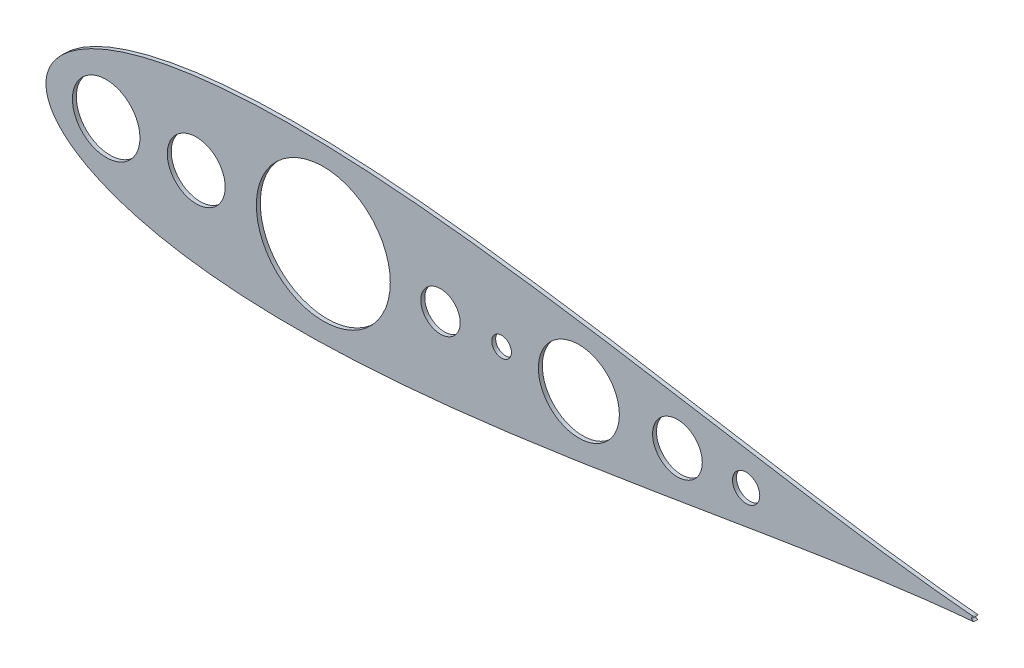
SolidWorks part; units mm, degrees
ref_plane "Front Plane" through (0, 0, 0) normal (0, 0, 1) x (1, 0, 0)
ref_plane "Top Plane" through (0, 0, 0) normal (0, 1, 0) x (1, 0, 0)
ref_plane "Right Plane" through (0, 0, 0) normal (1, 0, 0) x (0, 0, -1)
sketch "Model" plane through (0, 0, 0) normal (0, 0, 1) x (1, 0, 0)
  line L0 (786.347, 515.344) -> (786.347, 515.865)
  line L1 (784.9141, 514.1717) -> (785.37, 514.1717)
  line L2 (785.5654, 516.7117) -> (785.1095, 516.7117)
  line L3 (784.0675, 516.0604) -> (783.1903, 516.0604)
  line L4 (784.0675, 516.386) -> (784.0675, 516.0604)
  line L5 (783.2391, 516.386) -> (784.0675, 516.386)
  line L6 (783.4834, 518.0142) -> (783.2391, 516.386)
  line L7 (783.0906, 518.0142) -> (783.4834, 518.0142)
  line L8 (782.8463, 516.386) -> (783.0906, 518.0142)
  line L9 (782.0505, 518.0142) -> (781.8063, 516.386)
  line L10 (781.6577, 518.0142) -> (782.0505, 518.0142)
  line L11 (781.4135, 516.386) -> (781.6577, 518.0142)
  line L12 (780.4203, 516.386) -> (781.4135, 516.386)
  line L13 (780.4203, 516.0604) -> (780.4203, 516.386)
  line L14 (781.3647, 516.0604) -> (780.4203, 516.0604)
  line L15 (781.1886, 514.8881) -> (781.3647, 516.0604)
  line L16 (780.29, 514.8881) -> (781.1886, 514.8881)
  line L17 (780.29, 514.5625) -> (780.29, 514.8881)
  line L18 (781.1398, 514.5625) -> (780.29, 514.5625)
  line L19 (780.8762, 512.804) -> (781.1398, 514.5625)
  line L20 (781.27, 512.804) -> (780.8762, 512.804)
  line L21 (781.5336, 514.5625) -> (781.27, 512.804)
  line L22 (782.5726, 514.5625) -> (781.5336, 514.5625)
  line L23 (782.309, 512.804) -> (782.5726, 514.5625)
  line L24 (782.7028, 512.804) -> (782.309, 512.804)
  line L25 (782.9664, 514.5625) -> (782.7028, 512.804)
  line L26 (783.9372, 514.5625) -> (782.9664, 514.5625)
  line L27 (783.9372, 514.8881) -> (783.9372, 514.5625)
  line L28 (783.0153, 514.8881) -> (783.9372, 514.8881)
  line L29 (783.1903, 516.0604) -> (783.0153, 514.8881)
  line L30 (781.8063, 516.386) -> (782.8463, 516.386)
  line L31 (781.5824, 514.8881) -> (782.6214, 514.8881)
  line L32 (782.7975, 516.0604) -> (781.7575, 516.0604)
  line L33 (782.6214, 514.8881) -> (782.7975, 516.0604)
  line L34 (781.7575, 516.0604) -> (781.5824, 514.8881)
  circle A0 centre (390.1313, 511.9487) radius 18.669
  circle A1 centre (547.6113, 511.9487) radius 12.7
  circle A2 centre (586.9813, 511.9487) radius 6.35
  circle A3 centre (700.3234, 511.9487) radius 16.0288
  circle A4 centre (744.6175, 511.9487) radius 8.7799
  circle A5 centre (332.0731, 511.9487) radius 21.7634
  arc A6 (890.8162, 510.4774) -> (891.5484, 510.7448) centre (890.6938, 511.9487) ccw
  arc A7 (891.5489, 513.1522) -> (890.8162, 513.42) centre (890.6938, 511.9487) ccw
  arc A8 (891.5489, 513.1522) -> (891.5484, 510.7448) centre (891.2322, 511.9485) ccw
  circle A9 centre (636.7879, 511.9487) radius 26.1032
  circle A10 centre (472.0506, 511.9487) radius 43.167
  spline S0 degree 3 poles (890.8162, 513.42) (890.3349, 513.46) (886.7082, 513.7655) (879.5659, 514.4256) (868.9642, 515.5285) (857.2098, 516.8818) (844.3469, 518.4937) (830.4355, 520.3658) (815.5358, 522.4939) (799.7123, 524.867) (783.0322, 527.4682) (765.5654, 530.2744) (747.384, 533.2565) (728.5623, 536.3802) (709.1765, 539.6059) (689.3045, 542.8901) (669.0255, 546.185) (648.4208, 549.44) (627.5727, 552.6022) (606.5651, 555.6172) (585.4835, 558.4299) (564.4149, 560.9854) (543.4476, 563.23) (522.6717, 565.1117) (502.1785, 566.5817) (482.061, 567.5944) (462.4138, 568.109) (443.3327, 568.0899) (424.9152, 567.5068) (407.2601, 566.3367) (390.4682, 564.5628) (374.6421, 562.177) (359.8874, 559.1785) (346.3131, 555.5773) (334.0341, 551.3946) (323.1728, 546.6676) (313.8611, 541.4589) (306.2382, 535.8742) (300.4324, 530.0959) (296.5018, 524.4296) (294.31, 519.3174) (293.4249, 515.2165) (293.2233, 511.9487) (293.4249, 508.6808) (294.31, 504.5799) (296.5018, 499.4677) (300.4324, 493.8014) (306.2382, 488.0231) (313.8611, 482.4384) (323.1728, 477.2297) (334.0341, 472.5027) (346.3131, 468.32) (359.8874, 464.7188) (374.6421, 461.7204) (390.4682, 459.3346) (407.2601, 457.5606) (424.9152, 456.3906) (443.3327, 455.8074) (462.4138, 455.7883) (482.061, 456.3029) (502.1785, 457.3157) (522.6717, 458.7856) (543.4476, 460.6673) (564.4149, 462.9119) (585.4835, 465.4674) (606.5651, 468.2801) (627.5727, 471.2951) (648.4208, 474.4573) (669.0255, 477.7124) (689.3045, 481.0073) (709.1765, 484.2914) (728.5623, 487.5172) (747.384, 490.6408) (765.5654, 493.6229) (783.0322, 496.4291) (799.7123, 499.0303) (815.5358, 501.4035) (830.4355, 503.5316) (844.3469, 505.4037) (857.2098, 507.0155) (868.9642, 508.3689) (879.5659, 509.4717) (886.7082, 510.1319) (890.3349, 510.4373) (890.8162, 510.4774) knots 0.020157 0.020157 0.020157 0.020157 0.021271 0.028553 0.036781 0.04592 0.055932 0.066773 0.078397 0.090755 0.103793 0.117456 0.131686 0.146422 0.1616 0.177156 0.193024 0.209135 0.225421 0.241812 0.258238 0.274629 0.290914 0.307025 0.322893 0.338448 0.353626 0.368361 0.38259 0.396253 0.40929 0.421647 0.43327 0.444109 0.454119 0.463255 0.471479 0.478755 0.485052 0.490344 0.49461 0.497833 0.5 0.502167 0.50539 0.509656 0.514948 0.521245 0.528521 0.536745 0.545881 0.555891 0.56673 0.578353 0.59071 0.603747 0.61741 0.631639 0.646374 0.661552 0.677107 0.692975 0.709086 0.725371 0.741762 0.758188 0.774579 0.790865 0.806976 0.822844 0.8384 0.853578 0.868314 0.882544 0.896207 0.909245 0.921603 0.933227 0.944068 0.95408 0.963219 0.971447 0.978729 0.979843 0.979843 0.979843 0.979843
  spline S1 degree 3 poles (786.6085, 512.6737) (786.5542, 512.675) (786.4473, 512.6775) (786.2902, 512.6944) (786.1402, 512.7254) (785.9972, 512.767) (785.861, 512.8199) (785.732, 512.8856) (785.6095, 512.963) (785.4945, 513.0529) (785.3872, 513.1535) (785.2903, 513.2665) (785.2023, 513.3898) (785.1254, 513.525) (785.0563, 513.6702) (784.9994, 513.8273) (784.9494, 513.9949) (784.9261, 514.1118) (784.9141, 514.1717) knots 0 0 0 0 0.065541 0.128963 0.190377 0.250092 0.308548 0.366398 0.424542 0.48317 0.542243 0.601739 0.662506 0.724856 0.789128 0.856346 0.926295 1 1 1 1
  spline S2 degree 3 poles (786.6166, 513.1948) (786.6642, 513.1957) (786.7571, 513.1974) (786.8928, 513.2135) (787.0218, 513.2369) (787.1428, 513.273) (787.2574, 513.3177) (787.3639, 513.3738) (787.4638, 513.4396) (787.5557, 513.5144) (787.6383, 513.5963) (787.7111, 513.682) (787.773, 513.771) (787.8229, 513.864) (787.8623, 513.9604) (787.8891, 514.0607) (787.9078, 514.1639) (787.9093, 514.234) (787.91, 514.2694) knots 0 0 0 0 0.076072 0.148752 0.218403 0.28576 0.350598 0.414964 0.478069 0.541761 0.60435 0.664075 0.721464 0.777587 0.832644 0.887844 0.94346 1 1 1 1
  spline S3 degree 3 poles (785.7679, 513.4695) (785.7964, 513.4476) (785.8532, 513.4038) (785.9457, 513.3479) (786.0431, 513.2995) (786.1473, 513.2625) (786.2562, 513.2312) (786.3715, 513.2107) (786.4921, 513.1966) (786.5745, 513.1954) (786.6166, 513.1948) knots 0 0 0 0 0.118271 0.236178 0.355663 0.475904 0.600127 0.728608 0.861313 1 1 1 1
  spline S4 degree 3 poles (786.347, 515.865) (786.4098, 515.8661) (786.5329, 515.8682) (786.7127, 515.8934) (786.8847, 515.9284) (787.045, 515.9819) (787.1911, 516.0441) (787.3178, 516.1165) (787.4234, 516.1969) (787.5074, 516.2866) (787.5706, 516.3829) (787.6168, 516.4832) (787.6441, 516.5885) (787.6477, 516.6603) (787.6495, 516.6964) knots 0 0 0 0 0.110166 0.215787 0.318027 0.417574 0.51165 0.596162 0.672935 0.74367 0.810677 0.874059 0.936696 1 1 1 1
  spline S5 degree 3 poles (787.5122, 515.6493) (787.5662, 515.6232) (787.6733, 515.5715) (787.8192, 515.4701) (787.9517, 515.353) (788.0256, 515.2617) (788.0627, 515.2158) knots 0 0 0 0 0.25388 0.503009 0.750291 1 1 1 1
  spline S6 degree 3 poles (788.3659, 514.3131) (788.3633, 514.242) (788.3581, 514.1001) (788.3117, 513.8904) (788.2397, 513.6854) (788.1374, 513.4893) (788.0128, 513.3059) (787.8645, 513.1418) (787.6943, 513.0007) (787.5044, 512.8828) (787.2987, 512.7886) (787.0787, 512.7232) (786.8476, 512.6806) (786.6891, 512.6761) (786.6085, 512.6737) knots 0 0 0 0 0.079648 0.158922 0.239619 0.322609 0.406035 0.487602 0.569685 0.653036 0.737436 0.822478 0.909748 1 1 1 1
  spline S7 degree 3 poles (787.91, 514.2694) (787.9078, 514.3167) (787.9034, 514.4111) (787.8696, 514.5501) (787.8139, 514.6839) (787.736, 514.8104) (787.6412, 514.9277) (787.5303, 515.0323) (787.4026, 515.1186) (787.285, 515.1782) (787.1808, 515.2189) (787.0917, 515.246) (786.9919, 515.269) (786.8826, 515.2903) (786.7631, 515.3085) (786.6335, 515.3237) (786.4936, 515.3358) (786.3968, 515.3412) (786.347, 515.344) knots 0 0 0 0 0.066909 0.133485 0.201035 0.271234 0.34288 0.413836 0.485977 0.56023 0.599884 0.644055 0.691892 0.744688 0.801492 0.862858 0.929328 1 1 1 1
  spline S8 degree 3 poles (787.6495, 516.6964) (787.6489, 516.7229) (787.6477, 516.7757) (787.6326, 516.8528) (787.61, 516.9276) (787.5788, 516.9997) (787.5371, 517.0686) (787.4871, 517.1349) (787.4277, 517.1982) (787.3595, 517.2573) (787.2864, 517.3135) (787.2062, 517.3613) (787.1214, 517.4022) (787.0319, 517.4358) (786.9374, 517.4612) (786.8384, 517.4794) (786.7346, 517.4908) (786.6638, 517.4924) (786.6278, 517.4932) knots 0 0 0 0 0.055275 0.109966 0.163247 0.218076 0.273301 0.330909 0.390995 0.454176 0.518862 0.583311 0.648517 0.715031 0.782502 0.852323 0.924928 1 1 1 1
  spline S9 degree 3 poles (785.1095, 516.7117) (785.1219, 516.7628) (785.146, 516.8628) (785.1964, 517.0056) (785.2513, 517.1408) (785.3171, 517.2657) (785.389, 517.383) (785.4713, 517.4899) (785.5603, 517.5892) (785.6588, 517.6774) (785.762, 517.7572) (785.8715, 517.8252) (785.985, 517.8837) (786.1034, 517.9319) (786.2269, 517.9683) (786.3546, 517.9946) (786.4866, 518.0117) (786.5762, 518.0134) (786.6217, 518.0142) knots 0 0 0 0 0.072625 0.141977 0.208985 0.273957 0.336889 0.398745 0.460116 0.520825 0.580994 0.640152 0.698622 0.757271 0.816427 0.876254 0.937165 1 1 1 1
  spline S10 degree 3 poles (788.1054, 516.6944) (788.1037, 516.6407) (788.1004, 516.5356) (788.0724, 516.3821) (788.0251, 516.2375) (787.9597, 516.1011) (787.8751, 515.9738) (787.7725, 515.8552) (787.6513, 515.745) (787.5594, 515.6818) (787.5122, 515.6493) knots 0 0 0 0 0.128068 0.250608 0.37063 0.490072 0.610375 0.734313 0.863217 1 1 1 1
  spline S11 degree 3 poles (785.37, 514.1717) (785.3819, 514.1326) (785.405, 514.0565) (785.4443, 513.947) (785.4892, 513.8466) (785.5372, 513.7546) (785.5877, 513.6701) (785.6442, 513.5953) (785.7025, 513.5269) (785.7464, 513.4884) (785.7679, 513.4695) knots 0 0 0 0 0.14977 0.291316 0.425966 0.55216 0.671527 0.786122 0.895325 1 1 1 1
  spline S12 degree 3 poles (786.6278, 517.4932) (786.57, 517.4912) (786.457, 517.4873) (786.2941, 517.4527) (786.1427, 517.3976) (786.027, 517.3318) (785.9415, 517.2668) (785.8805, 517.2101) (785.8205, 517.1471) (785.7656, 517.0738) (785.71, 516.9954) (785.6594, 516.9077) (785.6103, 516.813) (785.5807, 516.7461) (785.5654, 516.7117) knots 0 0 0 0 0.122712 0.239685 0.351816 0.463766 0.520818 0.579448 0.640604 0.705298 0.773634 0.844669 0.920057 1 1 1 1
  spline S13 degree 3 poles (786.6217, 518.0142) (786.688, 518.0122) (786.8192, 518.0083) (787.0119, 517.9721) (787.1977, 517.9149) (787.3746, 517.8358) (787.539, 517.7383) (787.6852, 517.6223) (787.8113, 517.4899) (787.9171, 517.3437) (787.9999, 517.1874) (788.061, 517.0266) (788.0982, 516.8616) (788.103, 516.7502) (788.1054, 516.6944) knots 0 0 0 0 0.090254 0.17854 0.266093 0.354631 0.441886 0.525747 0.608114 0.690197 0.770821 0.848326 0.924012 1 1 1 1
  spline S14 degree 3 poles (788.0627, 515.2158) (788.0871, 515.1823) (788.1356, 515.1159) (788.1955, 515.0092) (788.2498, 514.9013) (788.2921, 514.7893) (788.3248, 514.6745) (788.3483, 514.5568) (788.3628, 514.436) (788.3649, 514.3542) (788.3659, 514.3131) knots 0 0 0 0 0.128136 0.254173 0.378112 0.501712 0.623986 0.747096 0.872875 1 1 1 1
sketch "Sketch2" plane through (0, 0, 0) normal (0, 0, 1) x (1, 0, 0)
  circle A0 centre (390.1313, 511.9487) radius 18.669
  circle A1 centre (547.6113, 511.9487) radius 12.7
  circle A2 centre (586.9813, 511.9487) radius 6.35
  circle A3 centre (700.3234, 511.9487) radius 16.0288
  circle A4 centre (744.6175, 511.9487) radius 8.7799
  circle A5 centre (332.0731, 511.9018) radius 21.7634
  arc A6 (890.8162, 510.4774) -> (891.5484, 510.7448) centre (890.6938, 511.9487) ccw
  arc A7 (891.5489, 513.1522) -> (890.8162, 513.42) centre (890.6938, 511.9487) ccw
  arc A8 (891.5489, 513.1522) -> (891.5484, 510.7448) centre (891.2322, 511.9485) ccw
  circle A9 centre (636.7879, 511.9487) radius 26.1032
  circle A10 centre (472.0506, 511.9018) radius 43.167
  spline S0 degree 3 poles (890.8162, 513.42) (890.3349, 513.46) (886.7082, 513.7655) (879.5659, 514.4256) (868.9642, 515.5285) (857.2098, 516.8818) (844.3469, 518.4937) (830.4355, 520.3658) (815.5358, 522.4939) (799.7123, 524.867) (783.0322, 527.4682) (765.5654, 530.2744) (747.384, 533.2565) (728.5623, 536.3802) (709.1765, 539.6059) (689.3045, 542.8901) (669.0255, 546.185) (648.4208, 549.44) (627.5727, 552.6022) (606.5651, 555.6172) (585.4835, 558.4299) (564.4149, 560.9854) (543.4476, 563.23) (522.6717, 565.1117) (502.1785, 566.5817) (482.061, 567.5944) (462.4138, 568.109) (443.3327, 568.0899) (424.9152, 567.5068) (407.2601, 566.3367) (390.4682, 564.5628) (374.6421, 562.177) (359.8874, 559.1785) (346.3131, 555.5773) (334.0341, 551.3946) (323.1728, 546.6676) (313.8611, 541.4589) (306.2382, 535.8742) (300.4324, 530.0959) (296.5018, 524.4296) (294.31, 519.3174) (293.4249, 515.2165) (293.2233, 511.9487) (293.4249, 508.6808) (294.31, 504.5799) (296.5018, 499.4677) (300.4324, 493.8014) (306.2382, 488.0231) (313.8611, 482.4384) (323.1728, 477.2297) (334.0341, 472.5027) (346.3131, 468.32) (359.8874, 464.7188) (374.6421, 461.7204) (390.4682, 459.3346) (407.2601, 457.5606) (424.9152, 456.3906) (443.3327, 455.8074) (462.4138, 455.7883) (482.061, 456.3029) (502.1785, 457.3157) (522.6717, 458.7856) (543.4476, 460.6673) (564.4149, 462.9119) (585.4835, 465.4674) (606.5651, 468.2801) (627.5727, 471.2951) (648.4208, 474.4573) (669.0255, 477.7124) (689.3045, 481.0073) (709.1765, 484.2914) (728.5623, 487.5172) (747.384, 490.6408) (765.5654, 493.6229) (783.0322, 496.4291) (799.7123, 499.0303) (815.5358, 501.4035) (830.4355, 503.5316) (844.3469, 505.4037) (857.2098, 507.0155) (868.9642, 508.3689) (879.5659, 509.4717) (886.7082, 510.1319) (890.3349, 510.4373) (890.8162, 510.4774) knots 0.020157 0.020157 0.020157 0.020157 0.021271 0.028553 0.036781 0.04592 0.055932 0.066773 0.078397 0.090755 0.103793 0.117456 0.131686 0.146422 0.1616 0.177156 0.193024 0.209135 0.225421 0.241812 0.258238 0.274629 0.290914 0.307025 0.322893 0.338448 0.353626 0.368361 0.38259 0.396253 0.40929 0.421647 0.43327 0.444109 0.454119 0.463255 0.471479 0.478755 0.485052 0.490344 0.49461 0.497833 0.5 0.502167 0.50539 0.509656 0.514948 0.521245 0.528521 0.536745 0.545881 0.555891 0.56673 0.578353 0.59071 0.603747 0.61741 0.631639 0.646374 0.661552 0.677107 0.692975 0.709086 0.725371 0.741762 0.758188 0.774579 0.790865 0.806976 0.822844 0.8384 0.853578 0.868314 0.882544 0.896207 0.909245 0.921603 0.933227 0.944068 0.95408 0.963219 0.971447 0.978729 0.979843 0.979843 0.979843 0.979843
  point P22 (0, 0)
  point P25 (304.3979, 511.9018)
  point P26 (0, 0)
extrude "Boss-Extrude1" add sketch "Sketch2" along normal blind 2.54
